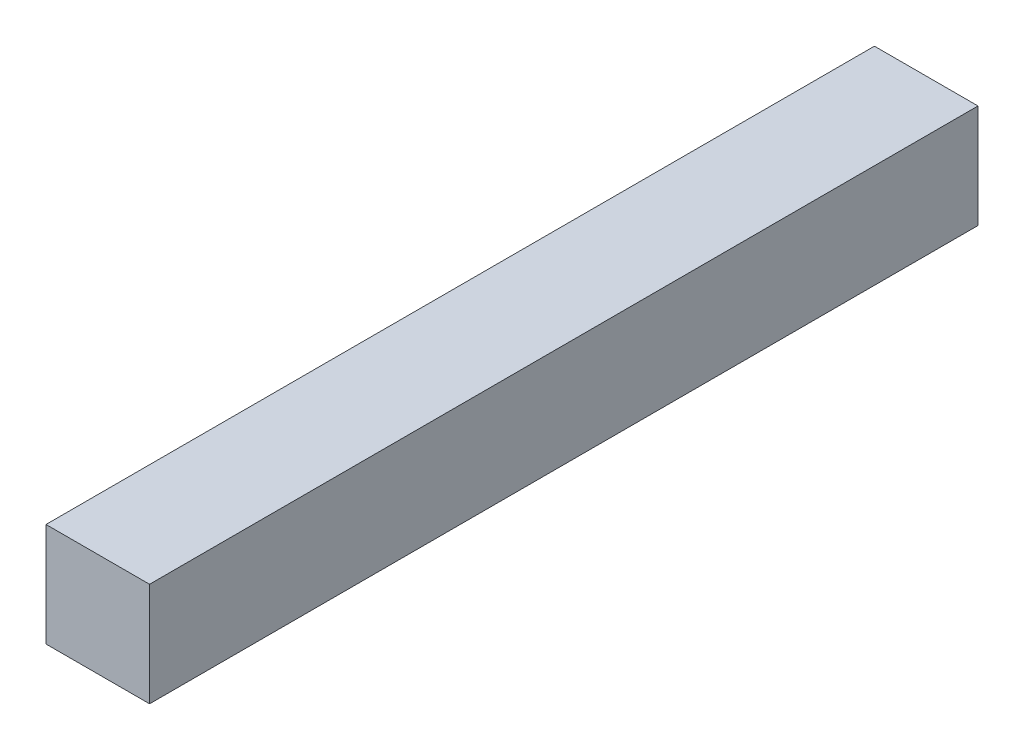
SolidWorks part; units mm, degrees
ref_plane "Front Plane" through (0, 0, 0) normal (0, 0, 1) x (1, 0, 0)
ref_plane "Top Plane" through (0, 0, 0) normal (0, 1, 0) x (1, 0, 0)
ref_plane "Right Plane" through (0, 0, 0) normal (1, 0, 0) x (0, 0, -1)
sketch "Sketch1" plane through (0, 0, 0) normal (0, 0, 1) x (1, 0, 0)
  line L1 (-19.05, 19.05) -> (19.05, 19.05)
  line L2 (-19.05, 19.05) -> (-19.05, -19.05)
  line L3 (-19.05, -19.05) -> (19.05, -19.05)
  line L4 (19.05, 19.05) -> (19.05, -19.05)
  line L5 (-19.05, 19.05) -> (19.05, -19.05) construction
  line L6 (-19.05, -19.05) -> (19.05, 19.05) construction
  point P0 (0, 0)
  dimension "D1" = 38.1
  dimension "D2" = 38.1
extrude "Boss-Extrude1" add sketch "Sketch1" against normal blind 304.8
